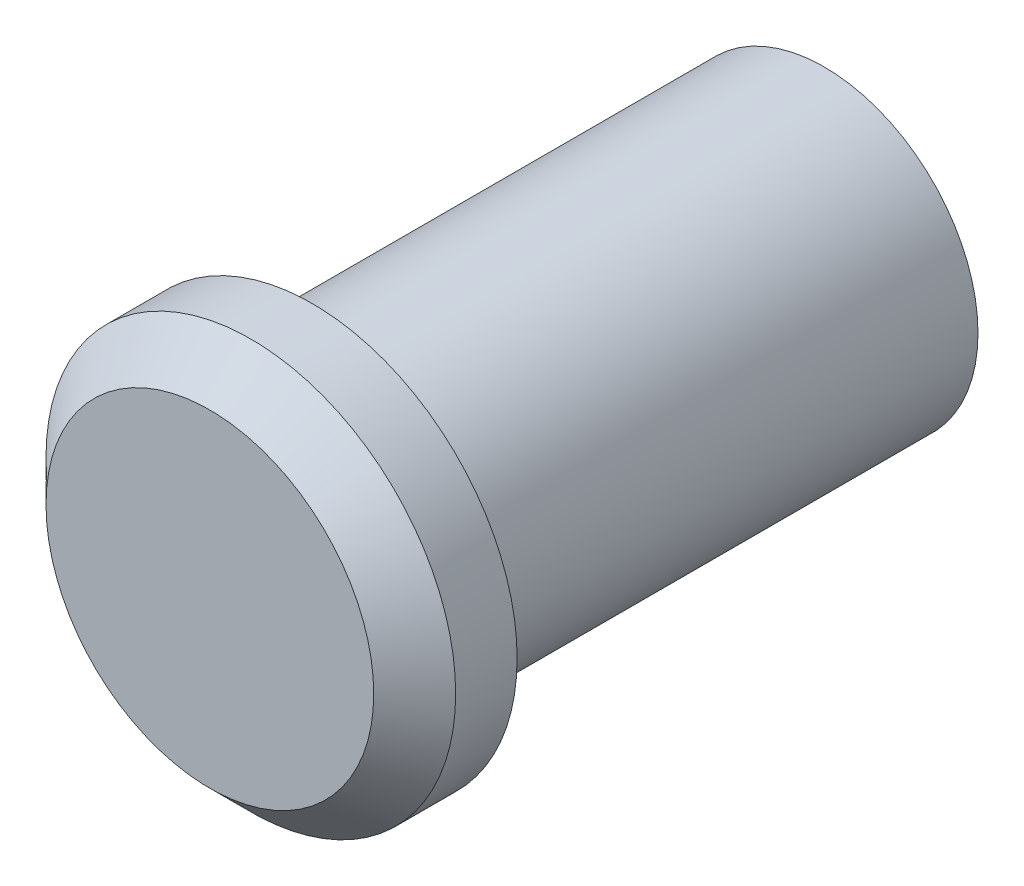
SolidWorks part; units mm, degrees
ref_plane "Front Plane" through (0, 0, 0) normal (0, 0, 1) x (1, 0, 0)
ref_plane "Top Plane" through (0, 0, 0) normal (0, 1, 0) x (1, 0, 0)
ref_plane "Right Plane" through (0, 0, 0) normal (1, 0, 0) x (0, 0, -1)
sketch "Sketch1" plane through (0, 0, 0) normal (0, 0, 1) x (1, 0, 0)
  circle A0 centre (0, 0) radius 7.5
  dimension "D1" = 15
extrude "Boss-Extrude1" add sketch "Sketch1" along normal blind 25
sketch "Sketch2" plane through (0, 0, 25) normal (0, 0, 1) x (1, 0, 0)
  circle A0 centre (0, 0) radius 10
  dimension "D1" = 20
extrude "Boss-Extrude2" add sketch "Sketch2" along normal blind 5
sketch "Sketch3" plane through (0, 0, 0) normal (0, 0, -1) x (-1, 0, 0)
  circle A0 centre (0, 0) radius 1.5
  dimension "D1" = 3
extrude "Cut-Extrude1" cut sketch "Sketch3" against normal blind 5 contours A0
chamfer "Chamfer1" distance 2 angle 45 1 edges at (10, 0, 30)
